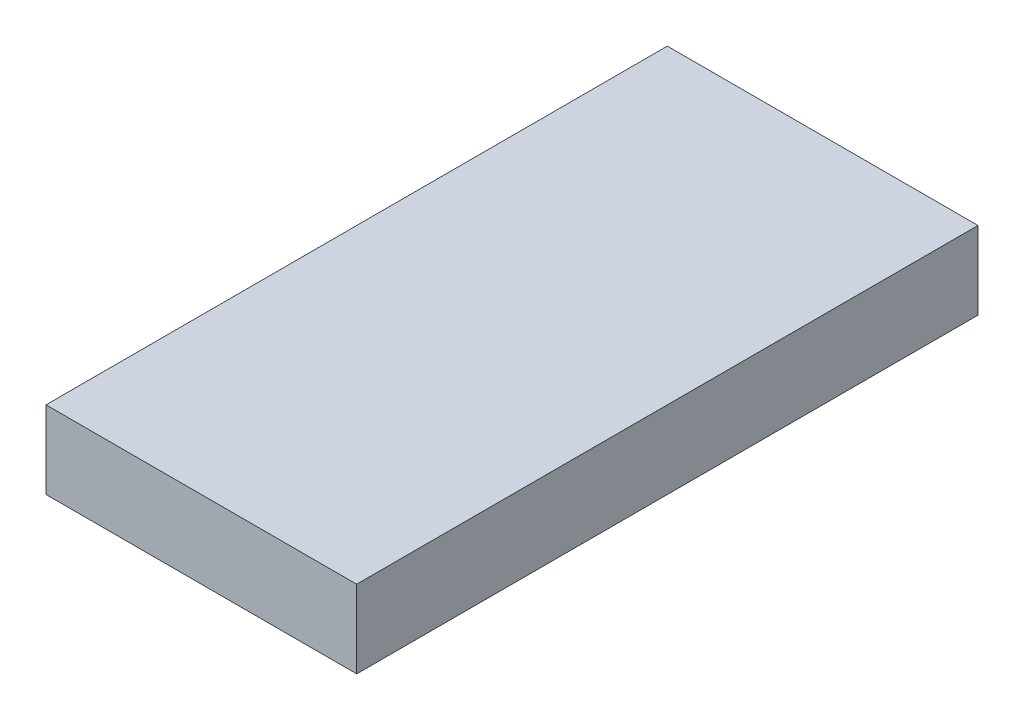
SolidWorks part; units mm, degrees
ref_plane "Front Plane" through (0, 0, 0) normal (0, 0, 1) x (1, 0, 0)
ref_plane "Top Plane" through (0, 0, 0) normal (0, 1, 0) x (1, 0, 0)
ref_plane "Right Plane" through (0, 0, 0) normal (1, 0, 0) x (0, 0, -1)
sketch "Sketch1" plane through (0, 0, 0) normal (0, 1, 0) x (1, 0, 0)
  line L1 (-1.5875, 3.175) -> (1.5875, 3.175)
  line L2 (-1.5875, 3.175) -> (-1.5875, -3.175)
  line L3 (-1.5875, -3.175) -> (1.5875, -3.175)
  line L4 (1.5875, 3.175) -> (1.5875, -3.175)
  line L5 (-1.5875, 3.175) -> (1.5875, -3.175) construction
  line L6 (-1.5875, -3.175) -> (1.5875, 3.175) construction
  point P0 (0, 0)
  dimension "D1" = 3.175
  dimension "D2" = 6.35
extrude "Boss-Extrude1" add sketch "Sketch1" along normal blind 0.7937
